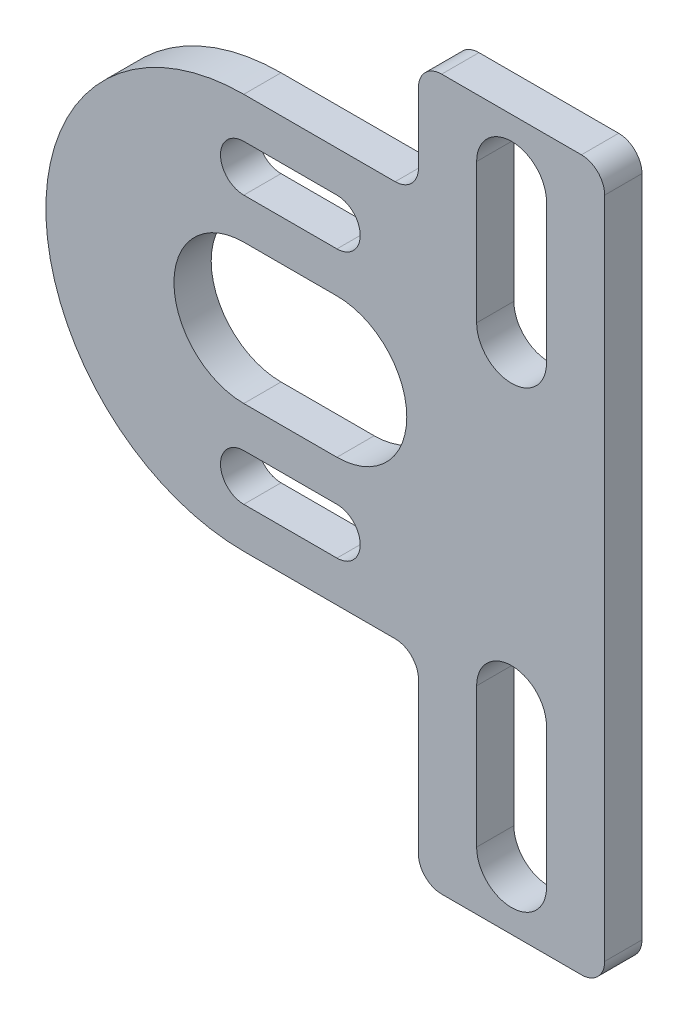
SolidWorks part; units mm, degrees
ref_plane "前视基准面" through (0, 0, 0) normal (0, 0, 1) x (1, 0, 0)
ref_plane "上视基准面" through (0, 0, 0) normal (0, 1, 0) x (1, 0, 0)
ref_plane "右视基准面" through (0, 0, 0) normal (1, 0, 0) x (0, 0, -1)
sketch "草图1" plane through (0, 0, 0) normal (0, 0, 1) x (1, 0, 0)
  line L0 (-6.5, 0) -> (6.5, 0) construction
  line L1 (0, -10.0356) -> (0, 17.2585) construction
  line L2 (-0.5, 0) -> (3.5, 0) construction
  line L3 (-0.5, 3) -> (3.5, 3)
  line L4 (-0.5, -3) -> (3.5, -3)
  line L5 (-0.5, 0) -> (3.5, 0) construction
  line L6 (-0.5, 8.5) -> (7, 8.5)
  line L7 (-0.5, -8.5) -> (7, -8.5)
  line L8 (7, -8.5) -> (7, -17)
  line L9 (7, -17) -> (15, -17)
  line L10 (11, -1.75) -> (15, -1.75) construction
  line L11 (15, -17) -> (15, 13.5)
  line L12 (-0.5, 5.75) -> (3.5, 5.75) construction
  line L13 (15, 13.5) -> (7, 13.5)
  line L14 (7, 13.5) -> (7, 8.5)
  line L15 (-0.5, 6.75) -> (3.5, 6.75)
  line L16 (-0.5, 4.75) -> (3.5, 4.75)
  line L17 (-0.5, 8.5) -> (-0.5, 3) construction
  line L18 (-0.5, -5.75) -> (3.5, -5.75) construction
  line L19 (-0.5, -6.75) -> (3.5, -6.75)
  line L20 (-0.5, -4.75) -> (3.5, -4.75)
  line L21 (11, -17) -> (11, 13.5) construction
  line L22 (11, -8.5) -> (11, -14.5) construction
  line L23 (12.5, -8.5) -> (12.5, -14.5)
  line L24 (9.5, -8.5) -> (9.5, -14.5)
  line L25 (11, 5) -> (11, 11) construction
  line L26 (12.5, 5) -> (12.5, 11)
  line L27 (9.5, 5) -> (9.5, 11)
  arc A0 (-0.5, 3) -> (-0.5, -3) centre (-0.5, 0) ccw
  arc A1 (-0.5, -6.75) -> (-0.5, -4.75) centre (-0.5, -5.75) cw
  arc A2 (-0.5, 8.5) -> (-0.5, -8.5) centre (-0.5, 0) ccw
  arc A3 (3.5, -4.75) -> (3.5, -6.75) centre (3.5, -5.75) cw
  arc A4 (-0.5, 6.75) -> (-0.5, 4.75) centre (-0.5, 5.75) ccw
  arc A5 (3.5, 4.75) -> (3.5, 6.75) centre (3.5, 5.75) ccw
  arc A6 (3.5, 3) -> (3.5, -3) centre (3.5, 0) cw
  arc A7 (12.5, -8.5) -> (9.5, -8.5) centre (11, -8.5) ccw
  arc A8 (9.5, -14.5) -> (12.5, -14.5) centre (11, -14.5) ccw
  arc A9 (12.5, 5) -> (9.5, 5) centre (11, 5) cw
  arc A10 (9.5, 11) -> (12.5, 11) centre (11, 11) cw
  point P7 (0, 0)
  point P14 (0, 0)
  point P16 (1.5, -5.75)
  point P28 (1.5, 5.75)
  point P42 (11, -11.5)
  point P49 (11, 8)
  dimension "D2" = 11.5
  dimension "D12" = 6
  dimension "D1" = 6
  dimension "D3" = 2
  dimension "D4" = 0.5
  dimension "D5" = 7
  dimension "D6" = 30.5
  dimension "D7" = 8
  dimension "D8" = 3
  dimension "D9" = 19.5
  dimension "D10" = 6
  dimension "D11" = 3.5
  dimension "D13" = 3
  dimension "D14" = 5
extrude "凸台-拉伸1" add sketch "草图1" along normal blind 1.6
fillet "圆角1" radius 1 6 edges at (7, 8.5, 0.8) (7, 13.5, 0.8) (7, -17, 0.8) (7, -8.5, 0.8) (15, 13.5, 0.8) (15, -17, 0.8)
